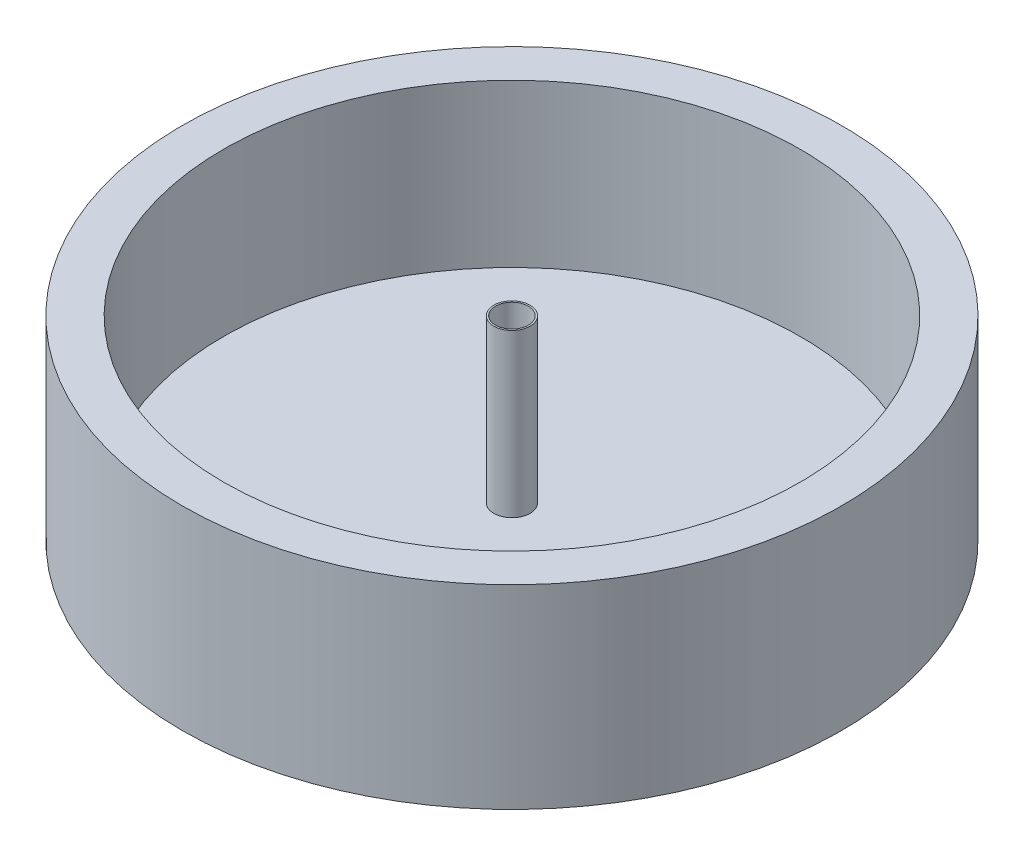
SolidWorks part; units mm, degrees
ref_plane "Front Plane" through (0, 0, 0) normal (0, 0, 1) x (1, 0, 0)
ref_plane "Top Plane" through (0, 0, 0) normal (0, 1, 0) x (1, 0, 0)
ref_plane "Right Plane" through (0, 0, 0) normal (1, 0, 0) x (0, 0, -1)
sketch "Sketch1" plane through (0, 0, 0) normal (0, 1, 0) x (1, 0, 0)
  circle A0 centre (0, 0) radius 50.8
  dimension "D1" = 101.6
extrude "Boss-Extrude2" add sketch "Sketch1" along normal blind 30
sketch "Sketch3" plane through (0, 30, 0) normal (0, 1, 0) x (1, 0, 0)
  circle A0 centre (0, 0) radius 44.45
  dimension "D1" = 88.9
extrude "Cut-Extrude1" cut sketch "Sketch3" against normal blind 25
sketch "Sketch4" plane through (0, 5, 0) normal (0, 1, 0) x (1, 0, 0)
  circle A0 centre (0, 0) radius 2.794
  dimension "D1" = 5.588
extrude "Boss-Extrude3" add sketch "Sketch4" along normal blind 25
sketch "Sketch5" plane through (0, 30, 0) normal (0, 1, 0) x (1, 0, 0)
  circle A0 centre (0, 0) radius 2.54
  dimension "D1" = 5.08
extrude "Cut-Extrude2" cut sketch "Sketch5" against normal blind 25
